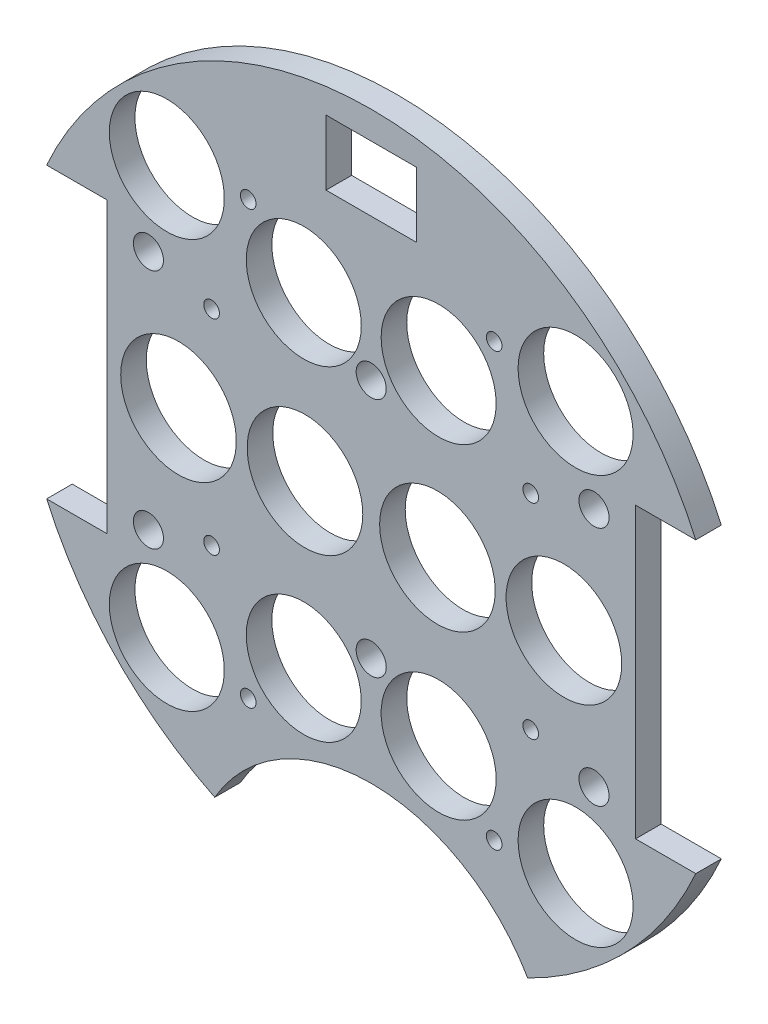
SolidWorks part; units mm, degrees
ref_plane "Front Plane" through (0, 0, 0) normal (0, 0, 1) x (1, 0, 0)
ref_plane "Top Plane" through (0, 0, 0) normal (0, 1, 0) x (1, 0, 0)
ref_plane "Right Plane" through (0, 0, 0) normal (1, 0, 0) x (0, 0, -1)
sketch "Sketch1" plane through (0, 0, 0) normal (0, 0, 1) x (1, 0, 0)
  line L0 (0, 0) -> (-82.1241, 0) construction
  line L1 (0, 0) -> (0, 95.6219) construction
  line L3 (-68.4505, 30.48) -> (-55.7505, 30.48)
  line L5 (-68.4505, -30.48) -> (-55.7505, -30.48)
  line L6 (-55.7505, 30.48) -> (-55.7505, -30.48)
  line L7 (68.4505, -30.48) -> (55.7505, -30.48)
  line L8 (68.4505, 30.48) -> (55.7505, 30.48)
  line L9 (55.7505, 30.48) -> (55.7505, -30.48)
  arc A0 (-68.4505, -30.48) -> (68.4505, -30.48) centre (0, 0) ccw
  arc A9 (68.4505, 30.48) -> (-68.4505, 30.48) centre (0, 0) ccw
  dimension "D6" = 60.96
  dimension "D7" = 12.7
  dimension "D8" = 74.93
  dimension "D9" = 74.93
  dimension "D11" = 30.48
extrude "Boss-Extrude2" add sketch "Sketch1" along normal blind 5.3975
sketch "Sketch3" plane through (0, 0, 0) normal (0, 0, -1) x (-1, 0, 0)
  line L0 (0, 0) -> (0, -116.2908) construction
  line L1 (0, 0) -> (-153.8039, 0) construction
  line L2 (0, 0) -> (15.2681, -56.9814) construction
  circle A0 centre (-13.97, 0) radius 12.192
  circle A1 centre (13.97, 0) radius 12.192
  circle A3 centre (40.64, 0) radius 12.192
  circle A4 centre (-43.1052, -43.1052) radius 12.1285
  circle A6 centre (14.224, -34.29) radius 12.1285
  circle A7 centre (14.224, 34.29) radius 12.1285
  circle A8 centre (-43.1052, 43.1052) radius 12.1285
  circle A11 centre (43.1052, 43.1052) radius 12.1285
  circle A12 centre (-14.224, 34.29) radius 12.1285
  circle A13 centre (-14.224, -34.29) radius 12.1285
  circle A14 centre (43.1052, -43.1052) radius 12.1285
  circle A15 centre (-40.64, 0) radius 12.192
  point P36 (0, 0)
  point P53 (0, 0)
  point P55 (0, 0)
  dimension "D1" = 24.384
  dimension "D2" = 0
  dimension "D3" = 14.224
  dimension "D4" = 15
  dimension "D5" = 34.29
  dimension "D6" = 24.384
  dimension "D7" = 0
  dimension "D8" = 24.257
  dimension "D9" = 40.64
  dimension "D10" = 13.97
extrude "Cut-Extrude2" cut sketch "Sketch3" against normal through all
sketch "Sketch5" plane through (0, 0, 0) normal (0, 0, -1) x (-1, 0, 0)
  line L0 (0, 0) -> (0, 43.5349) construction
  line L1 (9.525, 55.372) -> (-9.525, 55.372)
  line L2 (9.525, 55.372) -> (9.525, 69.088)
  line L3 (9.525, 69.088) -> (-9.525, 69.088)
  line L4 (-9.525, 55.372) -> (-9.525, 69.088)
  dimension "D1" = 19.05
  dimension "D2" = 13.716
  dimension "D3" = 55.372
extrude "Cut-Extrude3" cut sketch "Sketch5" against normal blind 40.64
sketch "Sketch6" plane through (0, 0, 5.3975) normal (0, 0, 1) x (1, 0, 0)
  line L0 (0, 0) -> (0, -136.4181) construction
  line L1 (-33.02, -67.2621) -> (33.02, -67.2621)
  circle A0 centre (0, 0) radius 74.93 construction
  circle A1 centre (0, -86.3121) radius 38.1
  arc M33 (-68.4505, -30.48) -> (68.4505, -30.48) centre (0, 0) ccw
  dimension "D4" = 76.2
  dimension "D5" = 0
  dimension "D6" = 19.05
  dimension "D1" = 74.93
  dimension "D2" = 74.93
  dimension "D3" = 66.04
extrude "Cut-Extrude4" cut sketch "Sketch6" against normal through all contours A1 L0 L1 | L0 A1 L1 | L0 L1 A1 M33 | L1 L0 A1 M33 | L0 A1 M33 | L0 A1 M33
extrude "Cut-Extrude5" cut sketch "Sketch7" against normal through all
sketch "Sketch7" plane through (-31.3134, 132.559, 12.7) normal (0, 0, 1) x (0, 1, 0)
  line L0 (-132.559, -31.3134) -> (-245.9178, -31.3134) construction
  line L1 (-132.559, -31.3134) -> (-132.559, -129.4011) construction
  circle A0 centre (-180.819, -4.6434) radius 1.651
  circle A3 centre (-180.819, -57.9834) radius 1.651
  circle A4 centre (-84.299, -57.9834) radius 1.651
  circle A5 centre (-84.299, -4.6434) radius 1.651
extrude "Cut-Extrude6" cut sketch "Sketch8" against normal through all both and the other way through all
sketch "Sketch8" plane through (-31.3134, 132.614, 44.45) normal (0, 0, 1) x (0, 1, 0)
  line L0 (-132.614, -31.3134) -> (-132.614, 57.8454) construction
  line L1 (-132.614, -31.3134) -> (-222.516, -31.3134) construction
  circle A0 centre (-158.014, 14.4066) radius 3.175
  circle A1 centre (-173.254, -31.3134) radius 3.175
  circle A3 centre (-158.014, -77.0334) radius 3.175
  circle A4 centre (-107.214, -77.0334) radius 3.175
  circle A5 centre (-91.974, -31.3134) radius 3.175
  circle A6 centre (-107.214, 14.4066) radius 3.175
extrude "Cut-Extrude9" cut sketch "Sketch11" against normal blind 75.692
sketch "Sketch11" plane through (30.092, 4.0835, -6.096) normal (0, 0, -1) x (-1, 0, 0)
  circle A0 centre (63.7572, 17.5065) radius 1.651
  circle A1 centre (63.7572, -25.6735) radius 1.651
  circle A2 centre (-3.5528, -25.6735) radius 1.651
  circle A3 centre (-3.5528, 17.5065) radius 1.651
extrude "Cut-Extrude11" cut sketch "Sketch13" against normal blind 97.79
sketch "Sketch13" plane through (30.092, 4.0835, -36.1315) normal (0, 0, -1) x (-1, 0, 0)
  line L0 (30.092, -29.4835) -> (30.092, 6.2385) construction
  circle A0 centre (4.1544, -49.7288) radius 1.651
  circle A4 centre (56.0296, -49.7288) radius 1.651
  circle A5 centre (4.1544, 41.3825) radius 1.651
  circle A9 centre (56.0296, 41.3825) radius 1.651
extrude "Cut-Extrude13" cut sketch "Sketch15" against normal blind 48.768 and the other way blind 103.378
sketch "Sketch15" plane through (30.092, 4.0835, 0) normal (0, 0, -1) x (-1, 0, 0)
  line L0 (30.092, -4.0835) -> (148.6336, -4.0835) construction
  line L1 (30.092, -4.0835) -> (30.092, 90.452) construction
  circle A0 centre (-16.898, 21.3165) radius 3.175
  circle A1 centre (77.082, 21.3165) radius 3.175
  circle A2 centre (30.092, 21.3165) radius 3.175
  circle A4 centre (77.082, -29.4835) radius 3.175
  circle A5 centre (30.092, -29.4835) radius 3.175
  circle A6 centre (-16.898, -29.4835) radius 3.175
